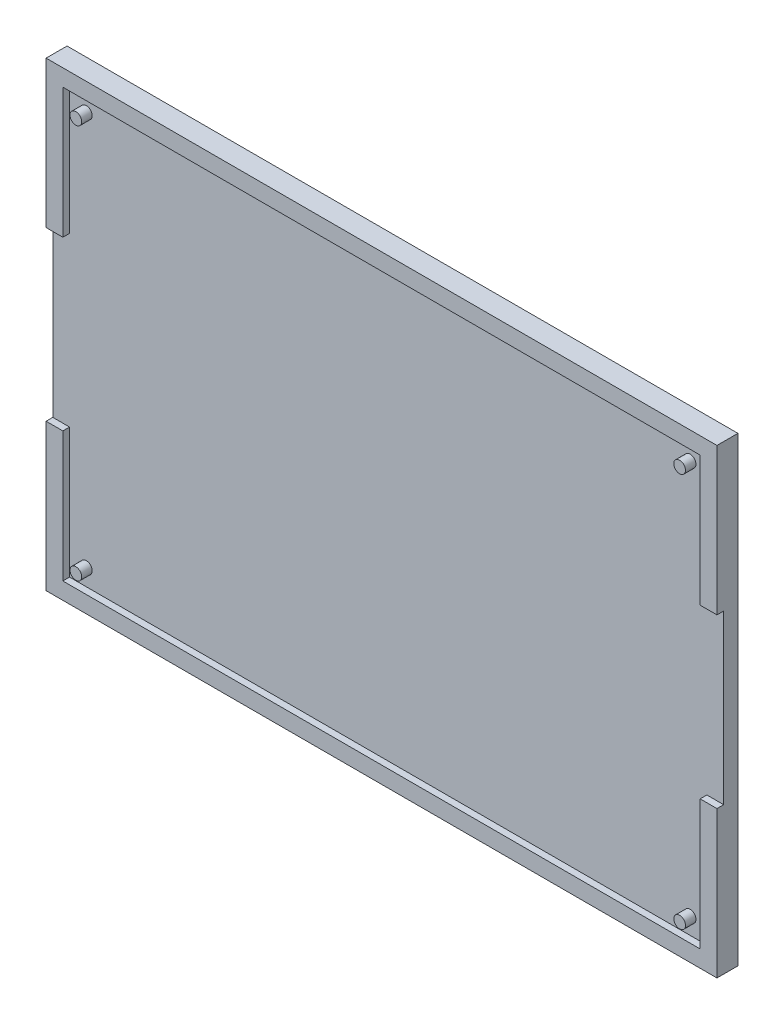
SolidWorks part; units mm, degrees
ref_plane "Front Plane" through (0, 0, 0) normal (0, 0, 1) x (1, 0, 0)
ref_plane "Top Plane" through (0, 0, 0) normal (0, 1, 0) x (1, 0, 0)
ref_plane "Right Plane" through (0, 0, 0) normal (1, 0, 0) x (0, 0, -1)
sketch "Sketch1" plane through (0, 0, 0) normal (0, 0, -1) x (1, 0, 0)
  line L1 (0, 0) -> (160, 0)
  line L2 (0, 0) -> (0, 110)
  line L3 (0, 110) -> (160, 110)
  line L4 (160, 0) -> (160, 110)
  dimension "D1" = 160
  dimension "D2" = 110
extrude "Boss-Extrude1" add sketch "Sketch1" against normal blind 5
sketch "Sketch3" plane through (0, 0, 5) normal (0, 0, 1) x (-1, 0, 0)
  line L1 (-156, 106) -> (-4, 106)
  line L2 (-156, 106) -> (-156, 4)
  line L3 (-156, 4) -> (-4, 4)
  line L4 (-4, 106) -> (-4, 4)
  line L5 (0, 0) -> (-160, 0) construction
  line L6 (-160, 0) -> (-160, 110) construction
  dimension "D1" = 152
  dimension "D2" = 102
  dimension "D3" = 4
  dimension "D4" = 4
extrude "Cut-Extrude1" cut sketch "Sketch3" against normal blind 1.6
sketch "Sketch4" plane through (0, 0, 3.4) normal (0, 0, 1) x (-1, 0, 0)
  line L0 (-4, 106) -> (-156, 106) construction
  line L1 (-156, 106) -> (-156, 4) construction
  line L2 (-4, 4) -> (-4, 106) construction
  line L3 (-156, 106) -> (-156, 4) construction
  line L4 (-156, 4) -> (-4, 4) construction
  circle A0 centre (-152, 102) radius 1.4
  circle A1 centre (-8, 102) radius 1.4
  circle A2 centre (-152, 8) radius 1.4
  circle A3 centre (-8, 8) radius 1.4
  dimension "D1" = 2.8
  dimension "D2" = 2.8
  dimension "D4" = 2.8
  dimension "D6" = 2.8
  dimension "D3" = 4
  dimension "D5" = 4
  dimension "D7" = 4
  dimension "D8" = 4
  dimension "D9" = 4
  dimension "D10" = 4
  dimension "D11" = 4
  dimension "D12" = 4
extrude "Boss-Extrude3" add sketch "Sketch4" along normal blind 2.5
sketch "Sketch11" plane through (0, 0, 5) normal (0, 0, 1) x (-1, 0, 0)
  line L0 (-156, 106) -> (-156, 4) construction
  line L1 (-156, 75) -> (-161, 75)
  line L2 (-156, 75) -> (-156, 35)
  line L3 (-156, 35) -> (-161, 35)
  line L4 (-161, 75) -> (-161, 35)
  line L5 (-156, 4) -> (-4, 4) construction
  line L8 (-4, 4) -> (-4, 106) construction
  line L9 (-4, 35) -> (1, 35)
  line L10 (-4, 35) -> (-4, 75)
  line L11 (-4, 75) -> (1, 75)
  line L12 (1, 35) -> (1, 75)
  line L13 (-4, 106) -> (-156, 106) construction
  dimension "D1" = 40
  dimension "D2" = 31
  dimension "D3" = 5
  dimension "D4" = 5
  dimension "D5" = 31
  dimension "D6" = 40
extrude "Cut-Extrude3" cut sketch "Sketch11" against normal blind 1.6
